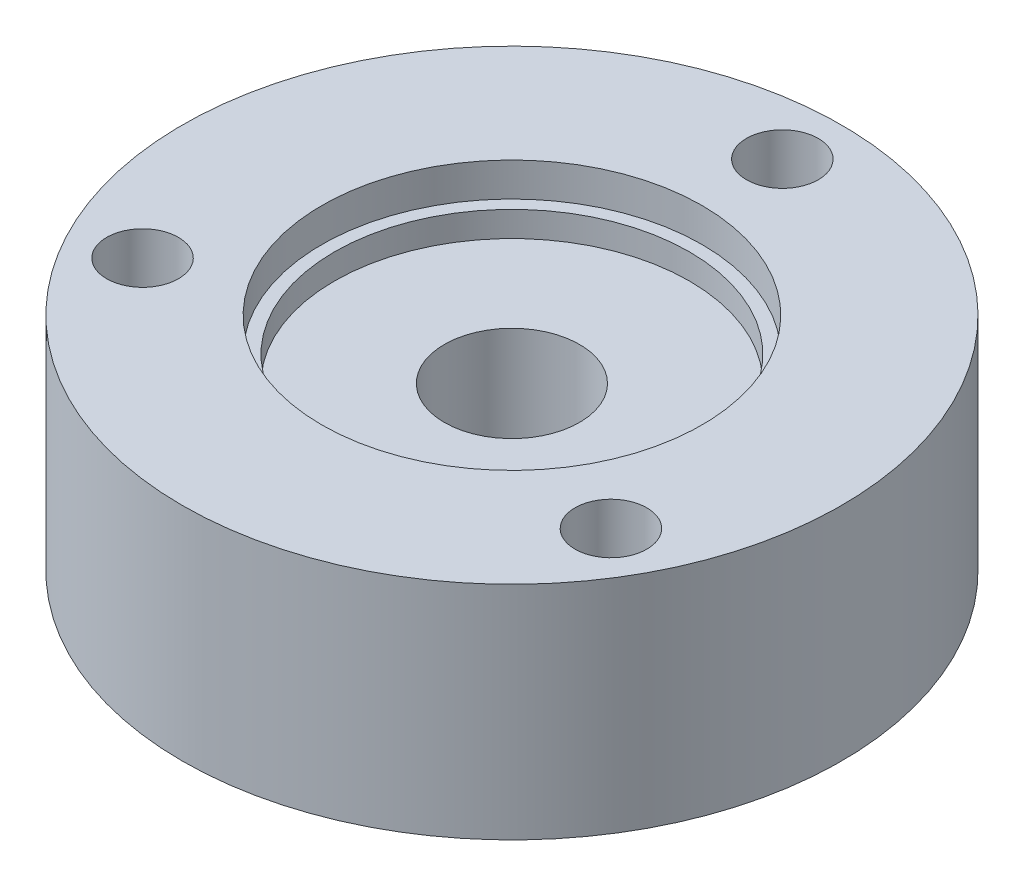
SolidWorks part; units mm, degrees
material "AISI 1018 Steel Cold Rolled"
ref_plane "Plane1" through (0, 0, 0) normal (0, 0, 1) x (1, 0, 0)
ref_plane "Plane2" through (0, 0, 0) normal (0, 1, 0) x (1, 0, 0)
ref_plane "Plane3" through (0, 0, 0) normal (1, 0, 0) x (0, 0, -1)
sketch "Sketch1" plane through (0, 0, 0) normal (0, 1, 0) x (1, 0, 0)
  circle A0 centre (0, 0) radius 61.9125
  dimension "D1" = 123.825
extrude "Base-Extrude" add sketch "Sketch1" along normal blind 7.9248 and the other way blind 33.6677
ref_plane "Plane4" through (0, 6.35, 0) normal (0, 1, 0) x (-1, 0, 0)
sketch "Sketch11" plane through (0, 6.35, 0) normal (0, 1, 0) x (-1, 0, 0)
  circle A0 centre (0, 0) radius 33.3375
  dimension "D1" = 66.675
extrude "Cut-Extrude1" cut sketch "Sketch11" against normal blind 9.525
sketch "Sketch12" plane through (0, 6.35, 0) normal (0, 1, 0) x (-1, 0, 0)
  circle A0 centre (0, 0) radius 35.7124
  dimension "D1" = 71.4248
extrude "Cut-Extrude2" cut sketch "Sketch12" against normal blind 4.7752 and the other way through all
sketch "Sketch13" plane through (0, 6.35, 0) normal (0, 1, 0) x (-1, 0, 0)
  circle A0 centre (0, 0) radius 12.7
  dimension "D1" = 25.4
extrude "Cut-Extrude3" cut sketch "Sketch13" against normal through all
sketch "Sketch32" plane through (0, 7.9248, 0) normal (0, 1, 0) x (-1, 0, 0)
  line L0 (0, 0) -> (0, -50.8) construction
  line L1 (0, 0) -> (43.9941, 25.4) construction
  line L2 (0, 0) -> (-43.9941, 25.4) construction
  circle A0 centre (0, 0) radius 50.8 construction
  circle A1 centre (0, -50.8) radius 6.7437
  circle A2 centre (-43.9941, 25.4) radius 6.7437
  circle A4 centre (43.9941, 25.4) radius 6.7437
  dimension "D2" = 120
  dimension "D3" = 120
  dimension "D4" = 3
  dimension "D1" = 101.6
  dimension "D5" = 13.4874
extrude "Cut-Extrude4" cut sketch "Sketch32" against normal blind 45.72
